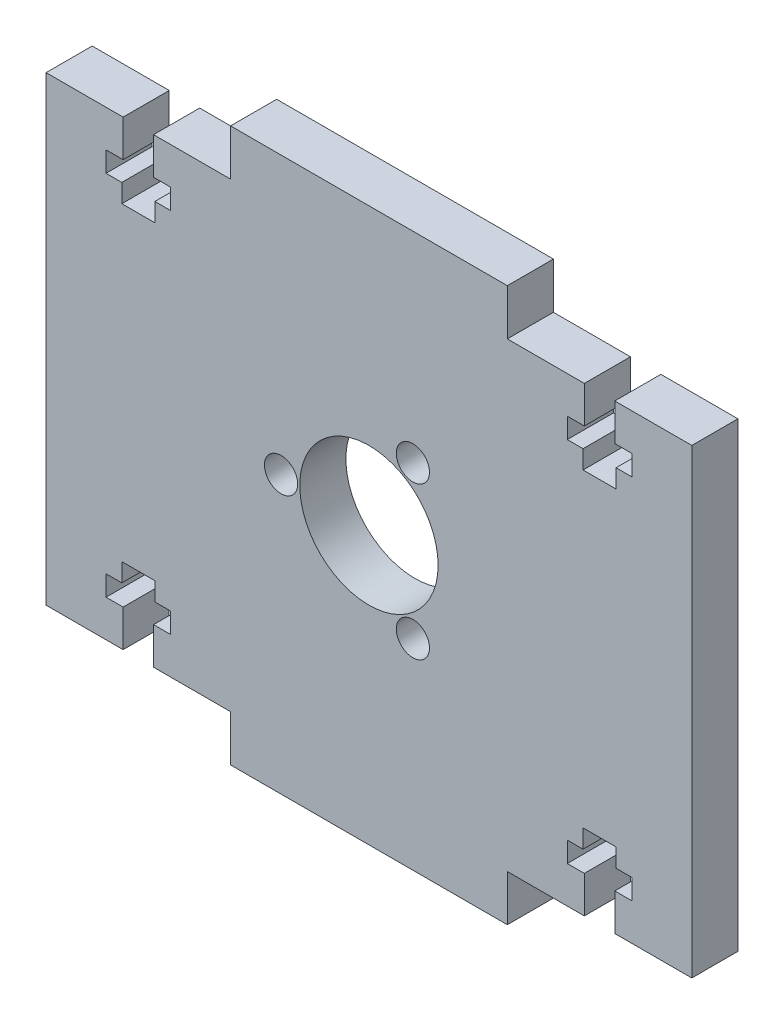
SolidWorks part; units mm, degrees
material "Acrylic (Medium-high impact)"
ref_plane "Front Plane" through (0, 0, 0) normal (0, 0, 1) x (1, 0, 0)
ref_plane "Top Plane" through (0, 0, 0) normal (0, 1, 0) x (1, 0, 0)
ref_plane "Right Plane" through (0, 0, 0) normal (1, 0, 0) x (0, 0, -1)
sketch "Sketch1" plane through (0, 0, 0) normal (0, 0, 1) x (1, 0, 0)
  line L0 (-61.9392, 0) -> (61.9392, 0) construction
  line L1 (0, -54.4916) -> (0, 54.4916) construction
  line L2 (-15, 30) -> (15, 30)
  line L3 (15, 30) -> (15, 25)
  line L4 (15, 25) -> (35, 25)
  line L5 (35, 25) -> (35, -25)
  line L6 (-35, 25) -> (-35, -25)
  line L7 (-15, 25) -> (-35, 25)
  line L8 (-15, 30) -> (-15, 25)
  line L9 (15, 30) -> (15, 25)
  line L10 (15, 25) -> (35, 25)
  line L11 (35, 25) -> (35, -25)
  line L12 (-35, 25) -> (-35, -25)
  line L13 (-15, 25) -> (-35, 25)
  line L14 (-15, 30) -> (-15, 25)
  line L15 (-15, -30) -> (-15, -25)
  line L16 (-15, -25) -> (-35, -25)
  line L17 (15, -25) -> (35, -25)
  line L18 (15, -30) -> (15, -25)
  line L19 (-15, -30) -> (-15, -25)
  line L20 (-15, -25) -> (-35, -25)
  line L21 (15, -25) -> (35, -25)
  line L22 (15, -30) -> (15, -25)
  line L23 (-15, -30) -> (15, -30)
  circle A0 centre (0, 0) radius 7.5
  circle A1 centre (4.7625, -8.2489) radius 1.8
  circle A2 centre (-9.525, 0) radius 1.8
  circle A3 centre (4.7625, 8.2489) radius 1.8
  point P9 (0, -30)
  point P11 (35, 0)
  point P14 (0, 30)
  point P15 (0, 0)
  point P21 (-35, 0)
  dimension "D5" = 15
  dimension "D1" = 50
  dimension "D2" = 5
  dimension "D3" = 30
  dimension "D4" = 70
extrude "Boss-Extrude1" add sketch "Sketch1" along normal blind 5 contours L15 L23 L18 L17 L5 L4 L3 L2 L8 L7 L6 L16
sketch "Sketch3" plane through (0, 0, 5) normal (0, 0, 1) x (1, 0, 0)
  line L0 (25, 25) -> (25, -25) construction
  line L1 (15, 25) -> (35, 25) construction
  line L2 (15, -25) -> (35, -25) construction
  line L3 (26.65, 25) -> (26.65, 21)
  line L4 (26.65, 21) -> (28.5, 21)
  line L5 (28.5, 21) -> (28.5, 18.8)
  line L6 (28.5, 18.8) -> (26.7886, 18.8)
  line L7 (26.7886, 18.8) -> (26.7886, 16.8)
  line L8 (26.7886, 16.8) -> (23.2114, 16.8)
  line L9 (26.65, 25) -> (23.35, 25)
  line L10 (23.2114, 18.8) -> (23.2114, 16.8)
  line L11 (21.5, 18.8) -> (23.2114, 18.8)
  line L12 (21.5, 21) -> (21.5, 18.8)
  line L13 (23.35, 21) -> (21.5, 21)
  line L14 (23.35, 25) -> (23.35, 21)
  line L15 (0, 30) -> (0, -30) construction
  line L16 (-15, 30) -> (15, 30) construction
  line L17 (-15, -30) -> (15, -30) construction
  line L18 (-35, 0) -> (35, 0) construction
  line L19 (-35, 25) -> (-35, -25) construction
  line L20 (35, 25) -> (35, -25) construction
  line L21 (-23.35, 25) -> (-23.35, 21)
  line L22 (-23.35, 21) -> (-21.5, 21)
  line L23 (-21.5, 21) -> (-21.5, 18.8)
  line L24 (-21.5, 18.8) -> (-23.2114, 18.8)
  line L25 (-23.2114, 18.8) -> (-23.2114, 16.8)
  line L26 (-26.65, 25) -> (-23.35, 25)
  line L27 (-26.7886, 16.8) -> (-23.2114, 16.8)
  line L28 (-26.7886, 18.8) -> (-26.7886, 16.8)
  line L29 (-28.5, 18.8) -> (-26.7886, 18.8)
  line L30 (-28.5, 21) -> (-28.5, 18.8)
  line L31 (-26.65, 21) -> (-28.5, 21)
  line L32 (-26.65, 25) -> (-26.65, 21)
  line L33 (-26.65, -25) -> (-26.65, -21)
  line L34 (-26.65, -21) -> (-28.5, -21)
  line L35 (-28.5, -21) -> (-28.5, -18.8)
  line L36 (-28.5, -18.8) -> (-26.7886, -18.8)
  line L37 (-26.7886, -18.8) -> (-26.7886, -16.8)
  line L38 (-26.7886, -16.8) -> (-23.2114, -16.8)
  line L39 (-26.65, -25) -> (-23.35, -25)
  line L40 (-23.2114, -18.8) -> (-23.2114, -16.8)
  line L41 (-21.5, -18.8) -> (-23.2114, -18.8)
  line L42 (-21.5, -21) -> (-21.5, -18.8)
  line L43 (-23.35, -21) -> (-21.5, -21)
  line L44 (-23.35, -25) -> (-23.35, -21)
  line L45 (23.35, -25) -> (23.35, -21)
  line L46 (23.35, -21) -> (21.5, -21)
  line L47 (21.5, -21) -> (21.5, -18.8)
  line L48 (21.5, -18.8) -> (23.2114, -18.8)
  line L49 (23.2114, -18.8) -> (23.2114, -16.8)
  line L50 (26.65, -25) -> (23.35, -25)
  line L51 (26.7886, -16.8) -> (23.2114, -16.8)
  line L52 (26.7886, -18.8) -> (26.7886, -16.8)
  line L53 (28.5, -18.8) -> (26.7886, -18.8)
  line L54 (28.5, -21) -> (28.5, -18.8)
  line L55 (26.65, -21) -> (28.5, -21)
  line L56 (26.65, -25) -> (26.65, -21)
  point P15 (25, 16.8)
  point P43 (-25, 16.8)
  point P68 (-25, -16.8)
  point P69 (25, -16.8)
  dimension "D1" = 4
  dimension "D2" = 2.2
  dimension "D3" = 2
  dimension "D4" = 3.3
  dimension "D5" = 7
extrude "Cut-Extrude1" cut sketch "Sketch3" against normal through all
